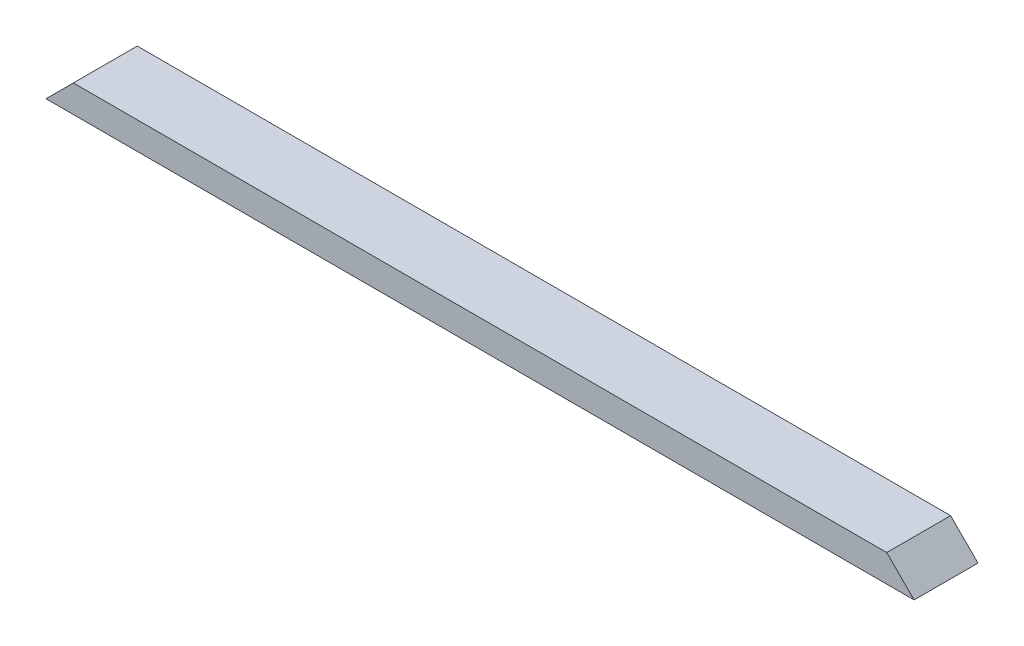
SolidWorks part; units mm, degrees
material "Pine"
ref_plane "Front Plane" through (0, 0, 0) normal (0, 0, 1) x (1, 0, 0)
ref_plane "Top Plane" through (0, 0, 0) normal (0, 1, 0) x (1, 0, 0)
ref_plane "Right Plane" through (0, 0, 0) normal (1, 0, 0) x (0, 0, -1)
sketch "Sketch1" plane through (0, 0, 0) normal (0, 1, 0) x (1, 0, 0)
  line L1 (0, 0) -> (1208.0875, 0)
  line L2 (0, 0) -> (0, 88.9)
  line L3 (0, 88.9) -> (1208.0875, 88.9)
  line L4 (1208.0875, 0) -> (1208.0875, 88.9)
  dimension "D1" = 88.9
  dimension "D2" = 1208.0875
extrude "Boss-Extrude1" add sketch "Sketch1" along normal blind 38.1
sketch "Sketch2" plane through (0, 0, 0) normal (0, 0, 1) x (1, 0, 0)
  line L0 (0, 0) -> (38.1, 38.1)
  line L1 (0, 38.1) -> (1208.0875, 38.1) construction
  line L2 (38.1, 38.1) -> (0, 38.1)
  line L3 (0, 38.1) -> (0, 0)
  line L5 (1208.0875, 0) -> (1208.0875, 38.1)
  line L9 (1208.0875, 38.1) -> (1169.9875, 38.1)
  line L10 (1169.9875, 38.1) -> (1208.0875, 0)
  dimension "D1" = 38.1
  dimension "D2" = 38.1
  dimension "D3" = 38.1
extrude "Cut-Extrude1" cut sketch "Sketch2" against normal through all
